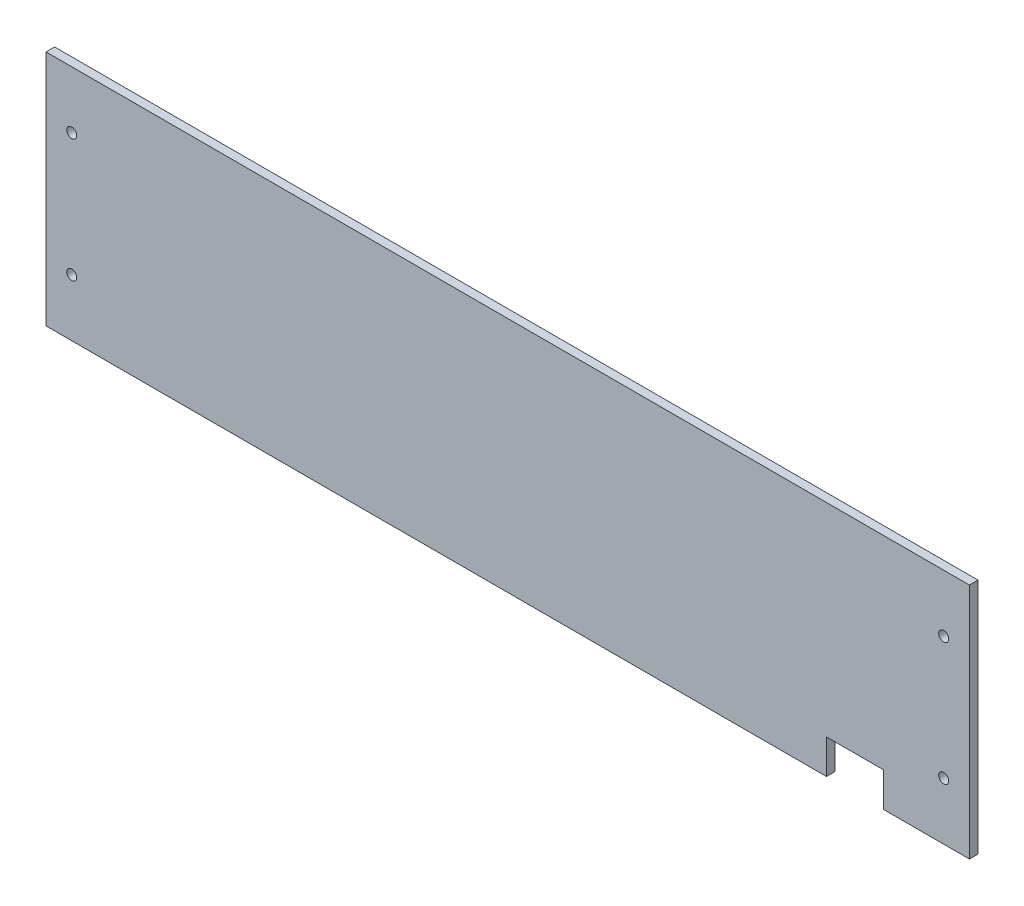
SolidWorks part; units mm, degrees
material "Acrylic (Medium-high impact)"
ref_plane "Front Plane" through (0, 0, 0) normal (0, 0, 1) x (1, 0, 0)
ref_plane "Top Plane" through (0, 0, 0) normal (0, 1, 0) x (1, 0, 0)
ref_plane "Right Plane" through (0, 0, 0) normal (1, 0, 0) x (0, 0, -1)
sketch "Sketch1" plane through (0, 0, 0) normal (0, 0, 1) x (1, 0, 0)
  line L1 (-161.5, 41.5) -> (161.5, 41.5)
  line L2 (-161.5, 41.5) -> (-161.5, -41.5)
  line L3 (-161.5, -41.5) -> (161.5, -41.5)
  line L4 (161.5, 41.5) -> (161.5, -41.5)
  line L5 (-161.5, 41.5) -> (161.5, -41.5) construction
  line L6 (-161.5, -41.5) -> (161.5, 41.5) construction
  point P0 (0, 0)
  dimension "D1" = 83
  dimension "D2" = 323
extrude "Boss-Extrude1" add sketch "Sketch1" along normal blind 3
sketch "Sketch2" plane through (0, 0, 0) normal (0, 0, -1) x (-1, 0, 0)
  line L0 (-131.5, -41.5) -> (-131.5, -29.5)
  line L1 (161.5, -41.5) -> (-161.5, -41.5) construction
  line L2 (-131.5, -29.5) -> (-111.5, -29.5)
  line L3 (-111.5, -29.5) -> (-111.5, -41.5)
  line L4 (-111.5, -41.5) -> (-131.5, -41.5)
  line L5 (-161.5, -41.5) -> (-161.5, 41.5) construction
  dimension "D1" = 20
  dimension "D2" = 12
  dimension "D3" = 30
extrude "Cut-Extrude1" cut sketch "Sketch2" against normal blind 10
sketch "Sketch4" plane through (0, 0, 0) normal (0, 0, -1) x (-1, 0, 0)
  line L0 (161.5, -41.5) -> (-111.5, -41.5) construction
  line L1 (161.5, 41.5) -> (161.5, -41.5) construction
  line L2 (-131.5, -41.5) -> (-161.5, -41.5) construction
  line L3 (-161.5, -41.5) -> (-161.5, 41.5) construction
  line L4 (-161.5, 41.5) -> (161.5, 41.5) construction
  circle A0 centre (152.5, -21.5) radius 1.75
  circle A1 centre (-152.5, -21.5) radius 1.75
  circle A2 centre (152.5, 21.5) radius 1.75
  circle A3 centre (-152.5, 21.5) radius 1.75
  point P18 (0, 0)
  point P20 (-161.5, 17.4752)
  dimension "D1" = 20
  dimension "D3" = 3.5
  dimension "D4" = 3.5
  dimension "D7" = 20
  dimension "D9" = 3.5
  dimension "D11" = 3.5
  dimension "D2" = 9
  dimension "D5" = 20
  dimension "D6" = 9
  dimension "D8" = 9
  dimension "D10" = 9
  dimension "D12" = 20
extrude "Cut-Extrude2" cut sketch "Sketch4" against normal through all
